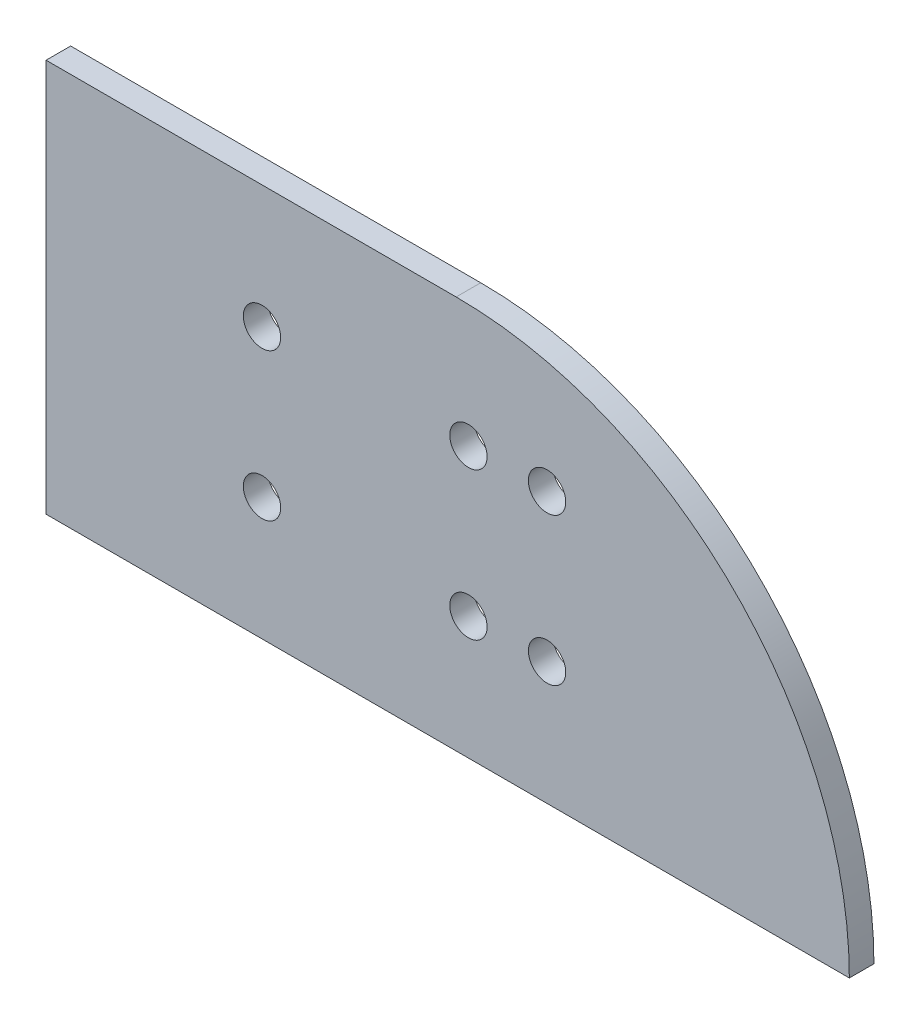
SolidWorks part; units mm, degrees
ref_plane "Front Plane" through (0, 0, 0) normal (0, 0, 1) x (1, 0, 0)
ref_plane "Top Plane" through (0, 0, 0) normal (0, 1, 0) x (1, 0, 0)
ref_plane "Right Plane" through (0, 0, 0) normal (1, 0, 0) x (0, 0, -1)
sketch "Sketch1" plane through (0, 0, 0) normal (0, 0, 1) x (1, 0, 0)
  line L0 (0, 50.8) -> (0, 0)
  line L1 (0, 0) -> (103.779, 0)
  line L3 (52.979, 50.8) -> (0, 50.8)
  arc A0 (103.779, 0) -> (52.979, 50.8) centre (52.979, 0) ccw
  point P0 (106.335, 34.0907)
  point P5 (88.9, 35.921)
  point P10 (0, 0)
  dimension "D1" = 88.9
  dimension "D2" = 50.8
  dimension "D3" = 103.779
extrude "Boss-Extrude1" add sketch "Sketch1" along normal blind 3.175
sketch "Sketch3" plane through (0, 0, 3.175) normal (0, 0, 1) x (1, 0, 0)
  line L0 (64.7265, 15.875) -> (54.5665, 15.875) construction
  line L1 (64.7265, 34.925) -> (54.5665, 34.925) construction
  circle A0 centre (64.7265, 15.875) radius 2.413 construction
  circle A1 centre (64.7265, 34.925) radius 2.413 construction
  circle A2 centre (27.8965, 15.875) radius 2.413 construction
  circle A3 centre (27.8965, 34.925) radius 2.413 construction
  circle A4 centre (64.7265, 15.875) radius 2.413
  circle A5 centre (64.7265, 34.925) radius 2.413
  circle A6 centre (27.8965, 15.875) radius 2.413
  circle A7 centre (27.8965, 34.925) radius 2.413
  circle A8 centre (54.5665, 34.925) radius 2.413
  circle A9 centre (54.5665, 15.875) radius 2.413
  dimension "D1" = 10.16
extrude "Cut-Extrude1" cut sketch "Sketch3" against normal through all and the other way through all
